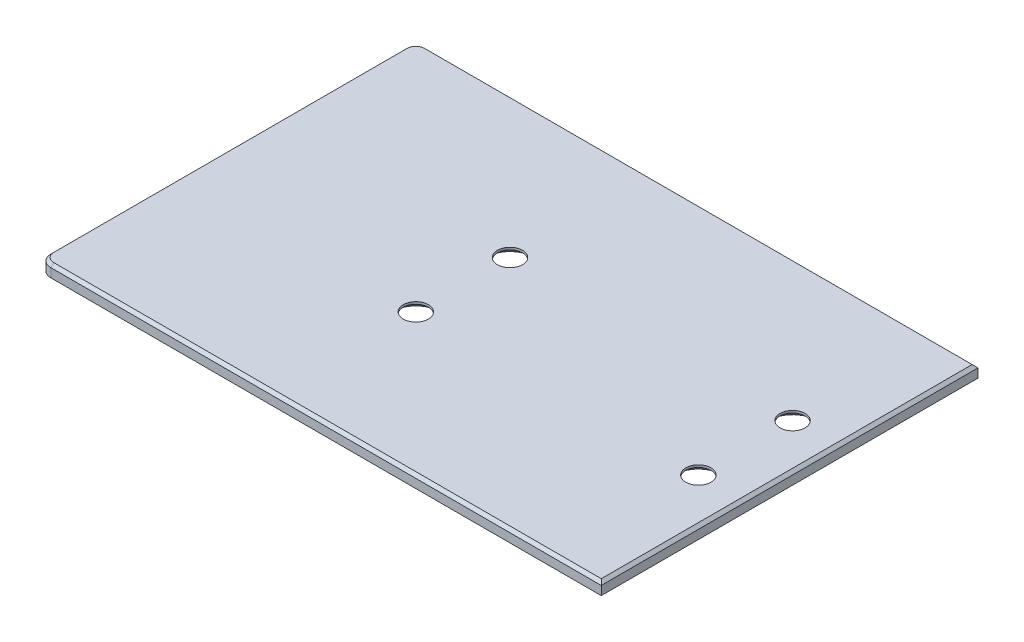
SolidWorks part; units mm, degrees
ref_plane "Front Plane" through (0, 0, 0) normal (0, 0, 1) x (1, 0, 0)
ref_plane "Top Plane" through (0, 0, 0) normal (0, 1, 0) x (1, 0, 0)
ref_plane "Right Plane" through (0, 0, 0) normal (1, 0, 0) x (0, 0, -1)
sketch "Sketch2" plane through (0, 0, 0) normal (0, 0, 1) x (1, 0, 0)
  line L1 (0, 0) -> (151.6062, 0)
  line L2 (0, 0) -> (0, -3.175)
  line L3 (0, -3.175) -> (151.6062, -3.175)
  line L4 (151.6062, 0) -> (151.6062, -3.175)
  dimension "D1" = 3.175
  dimension "D2" = 151.6062
extrude "Boss-Extrude2" add sketch "Sketch2" against normal blind 101.6
hole_wizard "CSK for 1/4 Flat Head Machine Screw (100)1" positions "Sketch3" profile "Sketch4" countersink size "1/4" standard "ANSI Inch" end condition through all
sketch "Sketch3" plane through (0, -3.175, 0) normal (0, -1, 0) x (-1, 0, 0)
  line L1 (0, 101.6) -> (0, 0) construction
  line L2 (-151.6062, 101.6) -> (-151.6062, 0) construction
  point P0 (-63.5, 38.1)
  point P2 (-63.5, 63.5)
  point P4 (-139.7, 63.5)
  point P6 (-139.7, 38.1)
  point P13 (0, 50.8)
  point P16 (-151.6062, 50.8)
  dimension "D1" = 12.7
  dimension "D2" = 12.7
  dimension "D3" = 11.9062
  dimension "D4" = 11.9062
  dimension "D5" = 12.7
  dimension "D6" = 12.7
  dimension "D7" = 63.5
  dimension "D8" = 63.5
sketch "Sketch4" plane through (63.5, -3.175, -38.1) normal (1, 0, 0) x (0, 0, -1)
  line L0 (0, 0) -> (0, 3.175)
  line L1 (0, 3.175) -> (3.3782, 3.175)
  line L2 (3.3782, 3.175) -> (3.3782, 2.5682)
  line L3 (3.3782, 2.5682) -> (6.4389, 0)
  line L5 (6.4389, 0) -> (0, 0)
  line L6 (-3.3782, 2.5682) -> (-6.4389, 0) construction
  line L11 (0, -6.35) -> (0, 107.95) construction
  dimension "Thru Hole Dia." = 6.7564
  dimension "Thru Hole Depth" = 3.175
  dimension "Near C'Sink Dia." = 12.8778
  dimension "Near C'Sink Angle" = 100
sketch "Sketch5" plane through (0, -3.175, 0) normal (0, -1, 0) x (1, 0, 0)
  line L0 (0, -101.6) -> (0, 0) construction
  line L1 (0, 0) -> (151.6062, 0) construction
  line L2 (0, -50.8) -> (-17.4068, -50.8) construction
  line L3 (3.175, 0) -> (0, 0)
  line L4 (0, 0) -> (0, -3.175)
  line L5 (0, -101.6) -> (0, -98.425)
  line L6 (3.175, -101.6) -> (0, -101.6)
  arc A0 (0, -3.175) -> (3.175, 0) centre (3.175, -3.175) cw
  arc A1 (0, -98.425) -> (3.175, -101.6) centre (3.175, -98.425) ccw
  dimension "D1" = 3.175
  dimension "D2" = 3.175
extrude "Cut-Extrude1" cut sketch "Sketch5" against normal through all
chamfer "Chamfer1" distance 0.7874 angle 45 6 edges at (0, 0, -50.8) (0.9299, 0, -100.6701) (0.9299, 0, -0.9299) (77.3906, 0, -101.6) (151.6062, 0, -50.8) (77.3906, 0, 0)
